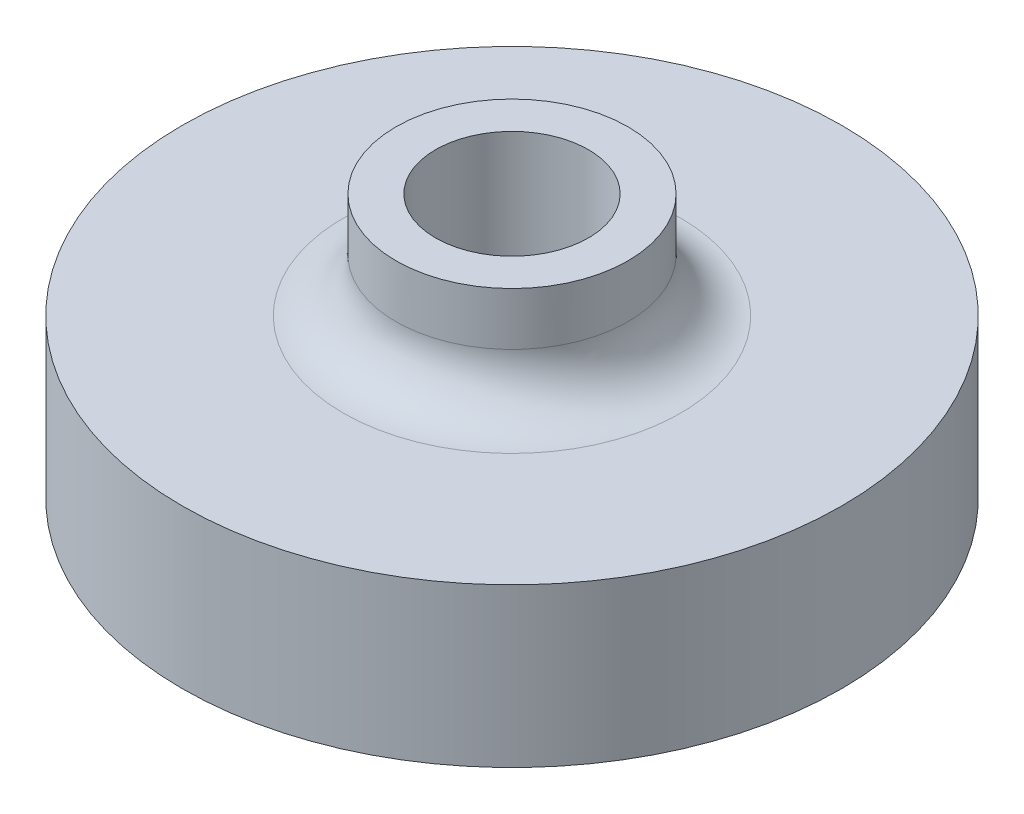
SolidWorks part; units mm, degrees
ref_plane "Front Plane" through (0, 0, 0) normal (0, 0, 1) x (1, 0, 0)
ref_plane "Top Plane" through (0, 0, 0) normal (0, 1, 0) x (1, 0, 0)
ref_plane "Right Plane" through (0, 0, 0) normal (1, 0, 0) x (0, 0, -1)
sketch "Sketch2" plane through (0, 0, 0) normal (0, 1, 0) x (1, 0, 0)
  circle A0 centre (0, 0) radius 9 construction
  circle A1 centre (0, 0) radius 11 construction
  arc A2 (-5.9772, 0.5229) -> (-2.5357, -5.4378) centre (0, 0) ccw construction
  arc A3 (-3.9848, 0.3486) -> (-1.6905, -3.6252) centre (0, 0) ccw construction
  circle A4 centre (0, 0) radius 1.25 construction
  arc A5 (-3.4415, 4.9149) -> (-2.2943, 3.2766) centre (-2.8679, 4.0958) ccw construction
  arc A6 (2.2943, 3.2766) -> (3.4415, 4.9149) centre (2.8679, 4.0958) ccw construction
  arc A7 (5.9772, 0.5229) -> (3.9848, 0.3486) centre (4.981, 0.4358) ccw construction
  arc A8 (1.6905, -3.6252) -> (2.5357, -5.4378) centre (2.1131, -4.5315) ccw construction
  arc A9 (-2.5357, -5.4378) -> (-1.6905, -3.6252) centre (-2.1131, -4.5315) ccw construction
  arc A10 (-3.9848, 0.3486) -> (-5.9772, 0.5229) centre (-4.981, 0.4358) ccw construction
  arc A11 (3.4415, 4.9149) -> (-3.4415, 4.9149) centre (0, 0) ccw construction
  arc A12 (2.2943, 3.2766) -> (-2.2943, 3.2766) centre (0, 0) ccw construction
  arc A13 (1.6905, -3.6252) -> (3.9848, 0.3486) centre (0, 0) ccw construction
  arc A14 (2.5357, -5.4378) -> (5.9772, 0.5229) centre (0, 0) ccw construction
  circle A15 centre (0, 0) radius 5 construction
sketch "Sketch3" plane through (0, 0, 0) normal (0, 1, 0) x (1, 0, 0)
  circle A0 centre (0, 0) radius 12.5
  dimension "D1" = 25
extrude "Boss-Extrude1" add sketch "Sketch3" along normal blind 10 contours A0
ref_plane "Plane1" through (0, 2, 0) normal (0, -1, 0) x (-1, 0, 0)
sketch "Sketch5" plane through (0, 2, 0) normal (0, -1, 0) x (-1, 0, 0)
  line L3 (9.4103, -3.701) -> (5.0801, -1.201)
  line L4 (7.9103, -6.299) -> (3.5801, -3.799)
  line L5 (1.5, 5) -> (1.5, 0)
  line L6 (0.75, -1.299) -> (-3.5801, -3.799)
  line L7 (-1.5, 5) -> (-1.5, 1.1547)
  line L8 (-5.0801, -1.201) -> (-1.75, 0.7217)
  circle A0 centre (0, 0) radius 5 construction
  arc A2 (1.5, 5) -> (-1.5, 5) centre (0, 5) ccw
  arc A3 (-5.0801, -1.201) -> (-3.5801, -3.799) centre (-4.3301, -2.5) ccw
  arc A5 (5.0801, -1.201) -> (3.5801, -3.799) centre (4.3301, -2.5) ccw
  arc A6 (7.8149, -6.2391) -> (9.3107, -3.6484) centre (8.6603, -5) ccw
  arc A7 (0.75, -1.299) -> (1.5, 0) centre (0, 0) ccw
  arc A8 (-1.5, 1.1547) -> (-1.75, 0.7217) centre (-2, 1.1547) cw
  dimension "D4" = 3
  dimension "D5" = 3
  dimension "D6" = 3
  dimension "D7" = 3
  dimension "D8" = 0.5
extrude "Cut-Extrude3" cut sketch "Sketch5" against normal blind 2.5
sketch "Sketch7" plane through (0, 2, 0) normal (0, -1, 0) x (-1, 0, 0)
  circle A0 centre (0, 5) radius 1.5
  circle A1 centre (-4.3301, -2.5) radius 1.5
  circle A2 centre (0, 0) radius 1.5
  circle A3 centre (8.6603, -5) radius 1.5
  circle A4 centre (4.3301, -2.5) radius 1.5
  dimension "D1" = 3
  dimension "D2" = 3
extrude "Cut-Extrude4" cut sketch "Sketch7" along normal through all
sketch "Sketch8" plane through (0, 10, 0) normal (0, 1, 0) x (1, 0, 0)
  circle A0 centre (0, 0) radius 2.9
  dimension "D1" = 5.8
extrude "Cut-Extrude5" cut sketch "Sketch8" against normal blind 4.5
sketch "Sketch9" plane through (0, 0, 0) normal (0, 0, 1) x (1, 0, 0)
  line L0 (0, -2.1729) -> (0, 19.9304) construction
  line L1 (2.9, 5.5) -> (2.9, 10) construction
  line L2 (21.4985, 15.0743) -> (4.4, 15.0743)
  line L3 (21.4985, 15.0743) -> (21.4985, 6)
  line L4 (21.4985, 6) -> (6.4, 6)
  line L5 (4.4, 15.0743) -> (4.4, 8)
  line L6 (21.4985, 15.0743) -> (4.4, 6) construction
  line L7 (21.4985, 6) -> (4.4, 15.0743) construction
  line L8 (3.5801, 4.5) -> (5.8301, 4.5) construction
  arc A0 (6.4, 6) -> (4.4, 8) centre (6.4, 8) cw
  point P3 (12.9493, 10.5371)
  dimension "D3" = 2
  dimension "D1" = 1.5
  dimension "D2" = 1.5
revolve "Cut-Revolve1" cut sketch "Sketch9" angle 360 about L0
